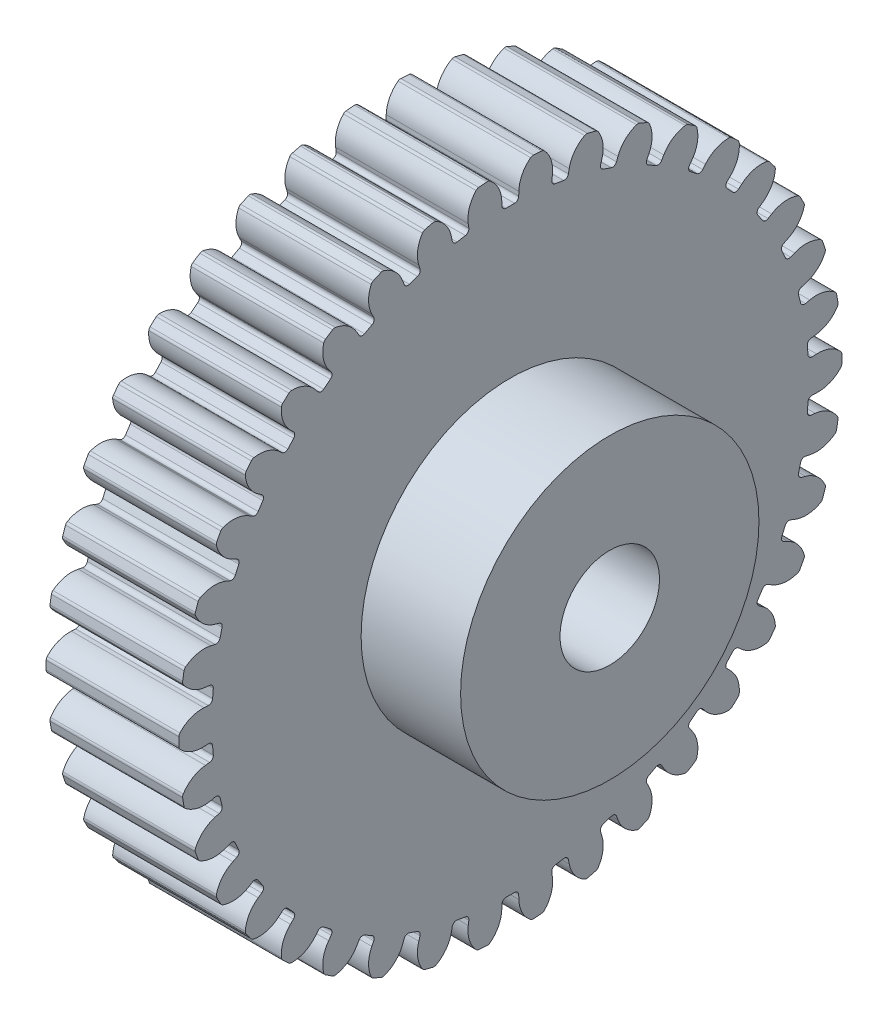
SolidWorks part; units mm, degrees
ref_plane "Plan de face" through (0, 0, 0) normal (0, 0, 1) x (1, 0, 0)
ref_plane "Plan de dessus" through (0, 0, 0) normal (0, 1, 0) x (1, 0, 0)
ref_plane "Plan de droite" through (0, 0, 0) normal (1, 0, 0) x (0, 0, -1)
sketch "Esquisse1" plane through (0, 0, 0) normal (1, 0, 0) x (0, 0, -1)
  circle A0 centre (0, 0) radius 20
  circle A1 centre (0, 0) radius 3
  dimension "D1" = 40
  dimension "D2" = 6
extrude "Extrusion1" add sketch "Esquisse1" along normal blind 8
sketch "Esquisse22" plane through (0, 0, 0) normal (-1, 0, 0) x (0, 0, 1)
  line L0 (0, 0) -> (0, 20) construction
  line L1 (-0.5, 18) -> (0.5, 18)
  line L2 (0.5, 18) -> (0.5139, 18.5)
  line L3 (0, 0) -> (-0.5, 18) construction
  line L4 (-0.5, 18) -> (-0.5139, 18.5)
  line L6 (-0.5139, 18.5) -> (0, 18.5) construction
  line L7 (-0.5139, 18.5) -> (-0.5553, 19.9923) construction
  circle A0 centre (0, 0) radius 20 construction
  arc A1 (-0.5139, 18.5) -> (-1.3053, 19.9574) centre (-2.345, 18.4491) ccw
  arc A2 (-1.3053, 19.9574) -> (1.3053, 19.9574) centre (0, 0) cw
  arc A3 (0.5139, 18.5) -> (1.3053, 19.9574) centre (2.345, 18.4491) cw
  point P13 (0, 18)
  dimension "D1" = 0.75
  dimension "D2" = 0.5
  dimension "D3" = 2
  dimension "D4" = 180
  dimension "D6" = 0.5
extrude "Enlèv. mat.-Extru.2" cut sketch "Esquisse22" against normal up to next (8 mm away)
fillet "Congé2" radius 0.25 4 edges at (4, 19.9574, 1.3053) (4, 18, 0.5) (4, 18, -0.5) (4, 19.9574, -1.3053)
pattern_circular "Répétition circulaire1" count 38 over 360 about axis through (0, 0, 0) along (1, 0, 0) of "Enlèv. mat.-Extru.2", "Congé2"
sketch "Esquisse23" plane through (8, 0, 0) normal (1, 0, 0) x (0, 0, -1)
  circle A0 centre (0, 0) radius 3
  circle A1 centre (0, 0) radius 9
  circle A2 centre (0, 0) radius 3 construction
  dimension "D1" = 18
extrude "Extrusion2" add sketch "Esquisse23" along normal blind 6
